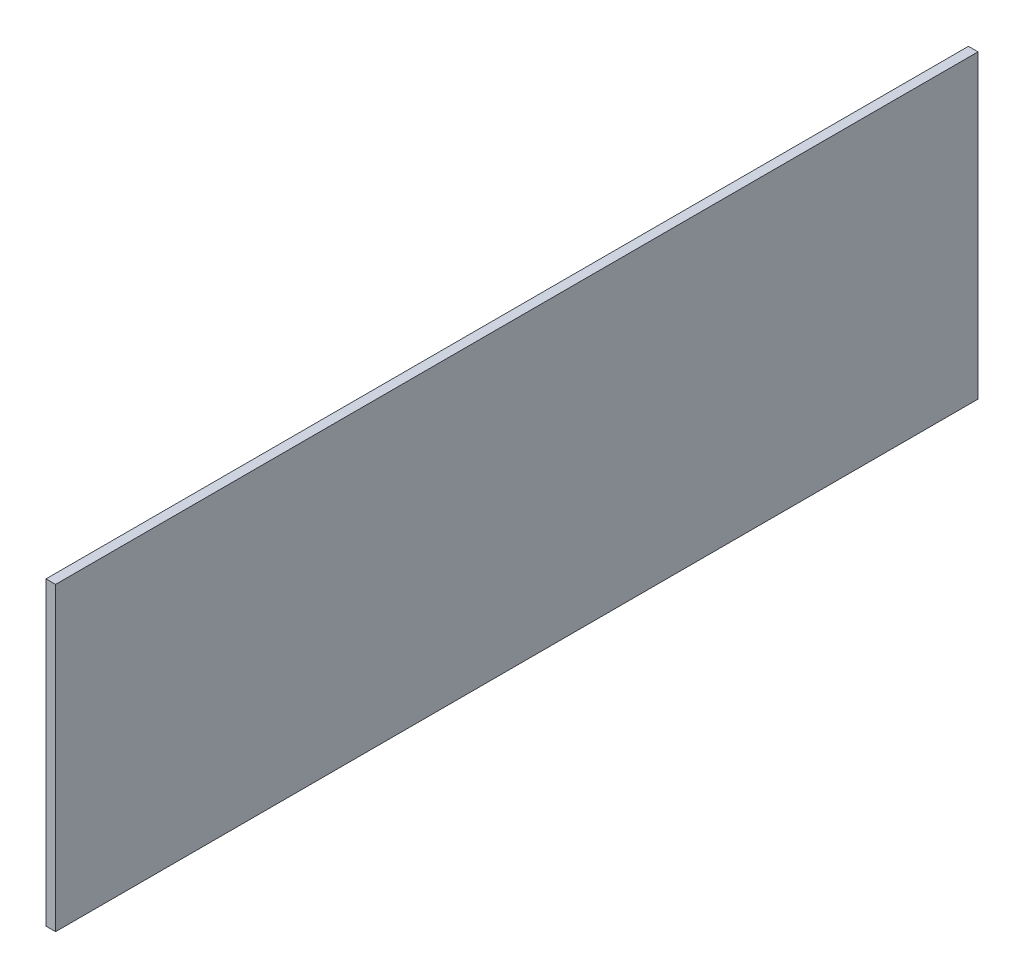
SolidWorks part; units mm, degrees
ref_plane "Front Plane" through (0, 0, 0) normal (0, 0, 1) x (1, 0, 0)
ref_plane "Top Plane" through (0, 0, 0) normal (0, 1, 0) x (1, 0, 0)
ref_plane "Right Plane" through (0, 0, 0) normal (1, 0, 0) x (0, 0, -1)
sketch "Sketch1" plane through (0, 0, 0) normal (1, 0, 0) x (0, 0, -1)
  line L0 (-187.325, 34.29) -> (104.775, 34.29)
  line L1 (104.775, -60.96) -> (-187.325, -60.96)
  line L2 (104.775, -60.96) -> (104.775, 34.29)
  line L4 (-187.325, -60.96) -> (-187.325, 34.29)
  line L5 (104.775, -60.96) -> (-58.9359, 34.29) construction
  line L6 (105.3703, 34.29) -> (-187.325, -60.96) construction
  point P0 (0, 0)
  dimension "D1" = 292.1
  dimension "D3" = 95.25
extrude "Boss-Extrude1" add sketch "Sketch1" along normal blind 3.03 contours L4 L0 L2 L1
